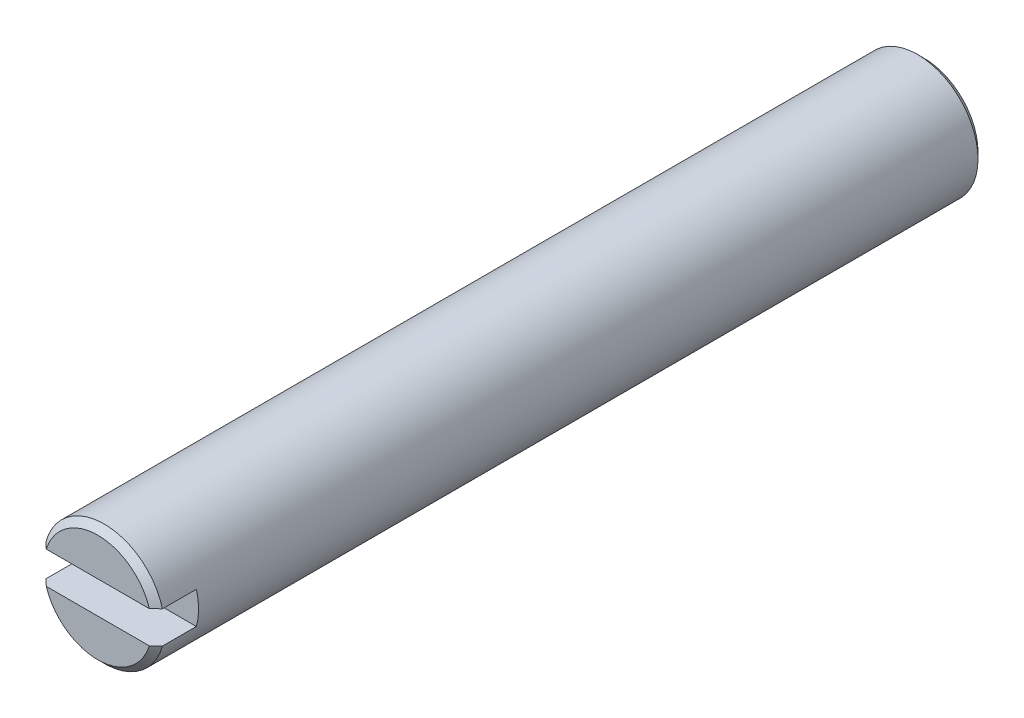
SolidWorks part; units mm, degrees
ref_plane "Front Plane" through (0, 0, 0) normal (0, 0, 1) x (1, 0, 0)
ref_plane "Top Plane" through (0, 0, 0) normal (0, 1, 0) x (1, 0, 0)
ref_plane "Right Plane" through (0, 0, 0) normal (1, 0, 0) x (0, 0, -1)
sketch "Sketch1" plane through (0, 0, 0) normal (0, 0, 1) x (1, 0, 0)
  line L1 (-1.8071, 0.5) -> (1.8071, 0.5)
  line L3 (-1.8071, -0.5) -> (1.8071, -0.5)
  circle A0 centre (0, 0) radius 1.875
  arc A1 (-1.8071, 0.5) -> (-1.8071, -0.5) centre (0, 0) cw
  arc A2 (1.8071, 0.5) -> (1.8071, -0.5) centre (0, 0) cw
  dimension "D1" = 3.75
extrude "Boss-Extrude1" add sketch "Sketch1" along normal blind 25.63 contours L1 A0 | L3 A0 | L1 A0 L3
sketch "Sketch2" plane through (0, 0, 25.63) normal (0, 0, 1) x (1, 0, 0)
  line L1 (-1.8071, 0.5) -> (1.8071, 0.5)
  line L3 (-1.8071, -0.5) -> (1.8071, -0.5)
  arc A0 (-1.8071, 0.5) -> (-1.8071, -0.5) centre (0, 0) ccw
  arc A1 (1.8071, -0.5) -> (1.8071, 0.5) centre (0, 0) ccw
  point P0 (0, 0)
extrude "Cut-Extrude1" cut sketch "Sketch2" against normal blind 1.25 contours L1 A1 L3 A0
chamfer "Chamfer1" distance 0.2 angle 45 1 edges at (0, -1.875, 25.63)
chamfer "Chamfer2" distance 0.2 angle 45 1 edges at (1.875, 0, 0)
